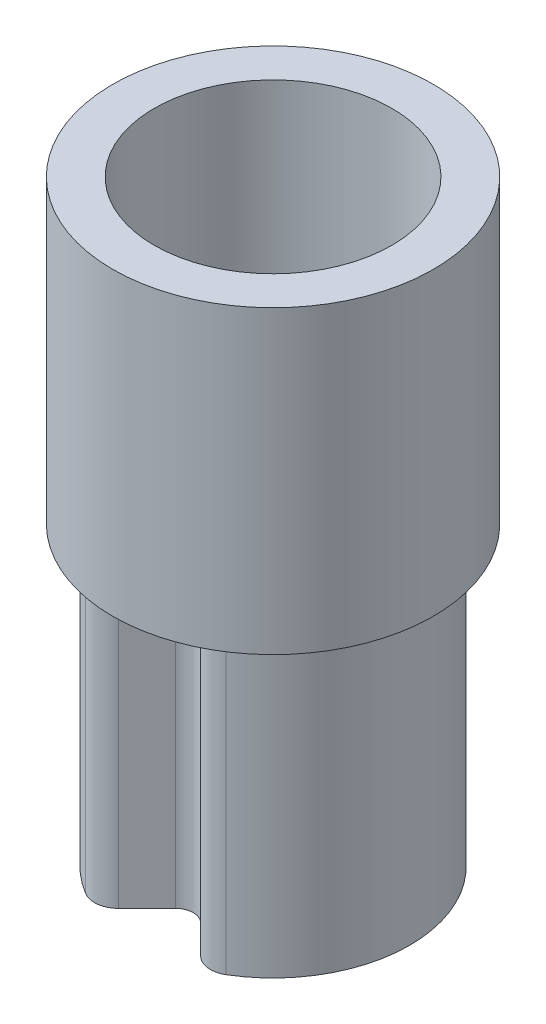
SolidWorks part; units mm, degrees
ref_plane "Front Plane" through (0, 0, 0) normal (0, 0, 1) x (1, 0, 0)
ref_plane "Top Plane" through (0, 0, 0) normal (0, 1, 0) x (1, 0, 0)
ref_plane "Right Plane" through (0, 0, 0) normal (1, 0, 0) x (0, 0, -1)
sketch "Sketch1" plane through (0, 0, 0) normal (0, 1, 0) x (1, 0, 0)
  line L0 (0, 0) -> (0, -1.15) construction
  line L1 (-0.4488, -1.0588) -> (-0.1061, -0.7161)
  line L2 (0.1061, -0.7161) -> (0.4488, -1.0588)
  line L3 (-0.4796, -0.8775) -> (-0.2121, -0.61)
  line L4 (0.2121, -0.61) -> (0.4796, -0.8775)
  arc A0 (0.4488, -1.0588) -> (-0.4488, -1.0588) centre (0, 0) ccw
  arc A1 (0.1061, -0.7161) -> (-0.1061, -0.7161) centre (0, -0.8221) ccw
  arc A2 (0.2121, -0.61) -> (-0.2121, -0.61) centre (0, -0.8221) ccw
  arc A3 (0.4796, -0.8775) -> (-0.4796, -0.8775) centre (0, 0) ccw
  point P8 (0, -0.61)
  dimension "D1" = 2.3
  dimension "D3" = 0.15
  dimension "D2" = 0.61
  dimension "D4" = 0.15
extrude "Boss-Extrude1" add sketch "Sketch1" along normal blind 2.5 contours A3 L3 A2 L4
fillet "Fillet1" radius 0.05 2 edges at (0.4796, 1.25, 0.8775) (-0.4796, 1.25, 0.8775)
fillet "Fillet2" radius 0.2 2 edges at (0.4488, 1.25, 1.0588) (-0.4488, 1.25, 1.0588)
sketch "Sketch2" plane through (0, 2.5, 0) normal (0, 1, 0) x (1, 0, 0)
  circle A0 centre (0, 0) radius 1.35
  circle A1 centre (0, 0) radius 1
  arc A2 (0.5136, -0.858) -> (-0.5136, -0.858) centre (0, 0) ccw construction
  dimension "D1" = 2.7
extrude "Boss-Extrude2" add sketch "Sketch2" along normal offset from surface (2.53 mm away) 5.03 up to face at (0, 0, 0.537)
